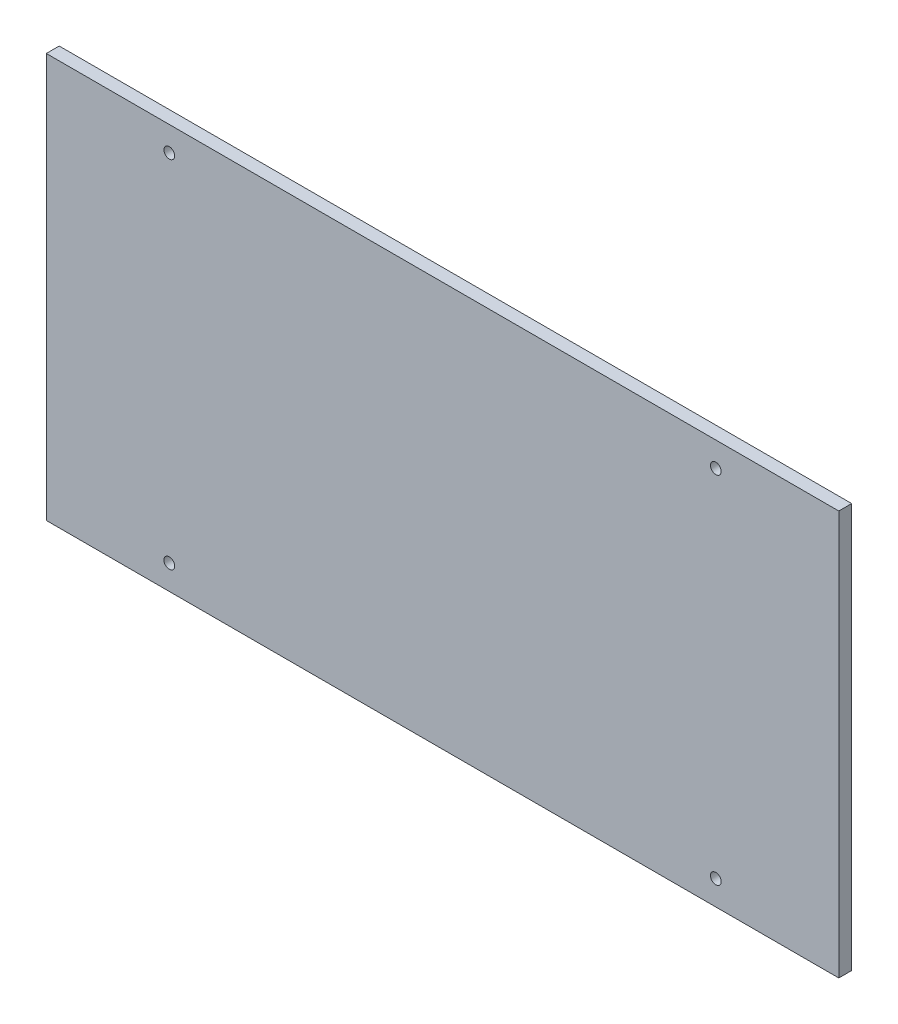
SolidWorks part; units mm, degrees
material "Acrylic (Medium-high impact)"
ref_plane "Front Plane" through (0, 0, 0) normal (0, 0, 1) x (1, 0, 0)
ref_plane "Top Plane" through (0, 0, 0) normal (0, 1, 0) x (1, 0, 0)
ref_plane "Right Plane" through (0, 0, 0) normal (1, 0, 0) x (0, 0, -1)
sketch "Sketch2" plane through (0, 0, 0) normal (0, 0, 1) x (1, 0, 0)
  line L1 (-92.075, -46.99) -> (92.075, -46.99)
  line L2 (-92.075, -46.99) -> (-92.075, 46.99)
  line L3 (-92.075, 46.99) -> (92.075, 46.99)
  line L4 (92.075, -46.99) -> (92.075, 46.99)
  line L5 (-92.075, -46.99) -> (92.075, 46.99) construction
  line L6 (-92.075, 46.99) -> (92.075, -46.99) construction
  line L7 (-63.5, -41.275) -> (63.5, -41.275) construction
  line L8 (-63.5, -41.275) -> (-63.5, 41.275) construction
  line L9 (-63.5, 41.275) -> (63.5, 41.275) construction
  line L10 (63.5, -41.275) -> (63.5, 41.275) construction
  line L11 (-63.5, -41.275) -> (63.5, 41.275) construction
  line L12 (-63.5, 41.275) -> (63.5, -41.275) construction
  circle A0 centre (-63.5, 41.275) radius 1.25
  circle A1 centre (63.5, -41.275) radius 1.25
  circle A2 centre (-63.5, -41.275) radius 1.25
  circle A3 centre (63.5, 41.275) radius 1.25
  point P0 (0, 0)
  point P5 (0, 0)
  dimension "D5" = 2.5
  dimension "D1" = 93.98
  dimension "D2" = 184.15
  dimension "D3" = 82.55
  dimension "D4" = 127
extrude "Boss-Extrude1" add sketch "Sketch2" along normal blind 3
